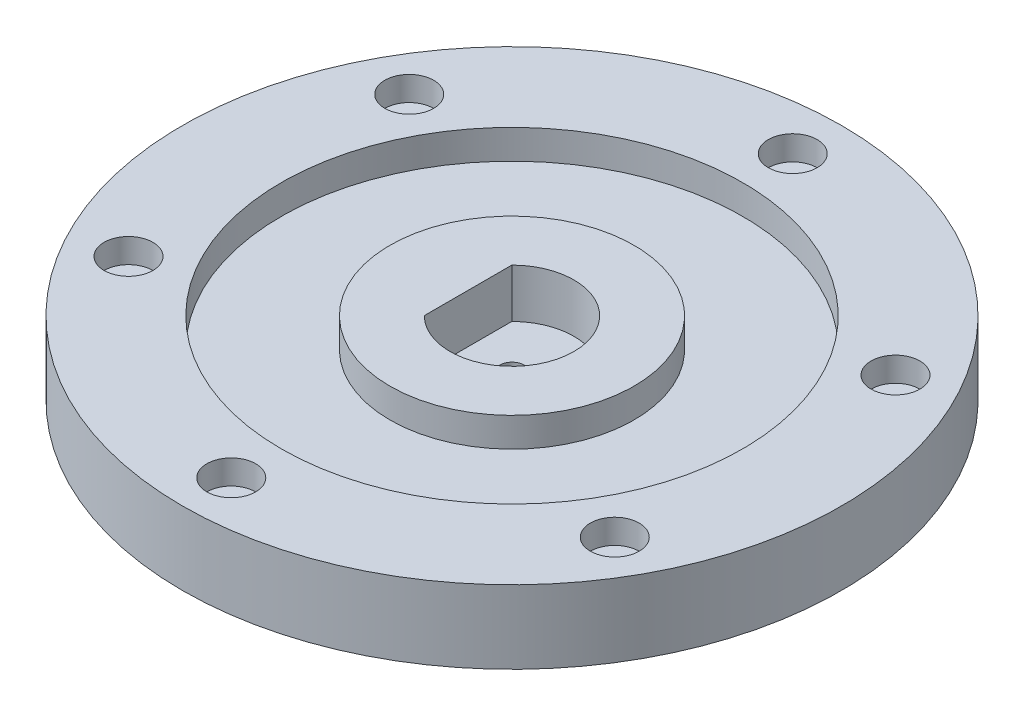
SolidWorks part; units mm, degrees
material "ABS"
ref_plane "Front Plane" through (0, 0, 0) normal (0, 0, 1) x (1, 0, 0)
ref_plane "Top Plane" through (0, 0, 0) normal (0, 1, 0) x (1, 0, 0)
ref_plane "Right Plane" through (0, 0, 0) normal (1, 0, 0) x (0, 0, -1)
sketch "Sketch1" plane through (0, 0, 0) normal (0, 1, 0) x (1, 0, 0)
  circle A0 centre (0, 0) radius 67.5
  dimension "D1" = 135
extrude "Boss-Extrude1" add sketch "Sketch1" along normal blind 15
sketch "Sketch2" plane through (0, 15, 0) normal (0, 1, 0) x (1, 0, 0)
  circle A0 centre (0, 0) radius 47.25
  circle A1 centre (0, 0) radius 25
  dimension "D1" = 94.5
  dimension "D2" = 50
extrude "Cut-Extrude1" cut sketch "Sketch2" against normal blind 6
sketch "Sketch3" plane through (0, 15, 0) normal (0, 1, 0) x (1, 0, 0)
  line L0 (-9, 8.9605) -> (-9, -8.9605)
  arc A0 (-9, -8.9605) -> (-9, 8.9605) centre (0, 0) ccw
  dimension "D1" = 25.4
  dimension "D2" = 9
extrude "Cut-Extrude2" cut sketch "Sketch3" against normal blind 10
sketch "Sketch5" plane through (0, 5, 0) normal (0, 1, 0) x (1, 0, 0)
  circle A0 centre (0, 0) radius 2.5
  dimension "D1" = 5
extrude "Cut-Extrude3" cut sketch "Sketch5" against normal blind 10
sketch "Sketch6" plane through (0, 15, 0) normal (0, 1, 0) x (1, 0, 0)
  circle A0 centre (0, 0) radius 57.5 construction
  circle A1 centre (0, 57.5) radius 2
  circle A2 centre (49.7965, 28.75) radius 2
  circle A3 centre (49.7965, -28.75) radius 2
  circle A4 centre (0, -57.5) radius 2
  circle A5 centre (-49.7965, -28.75) radius 2
  circle A6 centre (-49.7965, 28.75) radius 2
  point P17 (0, 0)
  dimension "D1" = 115
  dimension "D2" = 4
  dimension "D3" = 6
extrude "Cut-Extrude4" cut sketch "Sketch6" against normal blind 15
sketch "Sketch7" plane through (0, 15, 0) normal (0, 1, 0) x (1, 0, 0)
  circle A0 centre (0, 57.5) radius 5
  circle A1 centre (49.7965, 28.75) radius 5
  circle A2 centre (49.7965, -28.75) radius 5
  circle A3 centre (0, -57.5) radius 5
  circle A4 centre (-49.7965, -28.75) radius 5
  circle A5 centre (-49.7965, 28.75) radius 5
  point P15 (0, 0)
  dimension "D1" = 10
  dimension "D2" = 6
extrude "Cut-Extrude5" cut sketch "Sketch7" against normal blind 5
sketch "Sketch8" plane through (0, 0, 0) normal (0, -1, 0) x (1, 0, 0)
  line L0 (-80.8317, 45) -> (94.025, 45) construction
  line L1 (0, 0) -> (116.8808, 0) construction
  line L2 (-25, 57.9507) -> (-25, -4.8565) construction
  line L3 (-45, 66.6842) -> (-45, -9.502) construction
  line L4 (25, 59.4372) -> (25, -12.1035) construction
  line L5 (45, 59.4372) -> (45, -15.6341) construction
  circle A0 centre (-25, 45) radius 2
  circle A1 centre (-45, 45) radius 2
  circle A2 centre (25, 45) radius 2
  circle A3 centre (45, 45) radius 2
  circle A4 centre (45, -45) radius 2
  circle A5 centre (25, -45) radius 2
  circle A6 centre (-25, -45) radius 2
  circle A7 centre (-45, -45) radius 2
  dimension "D6" = 4
  dimension "D7" = 4
  dimension "D8" = 4
  dimension "D9" = 4
  dimension "D1" = 45
  dimension "D2" = 25
  dimension "D3" = 20
  dimension "D4" = 25
  dimension "D5" = 20
extrude "Cut-Extrude6" cut sketch "Sketch8" against normal blind 10
